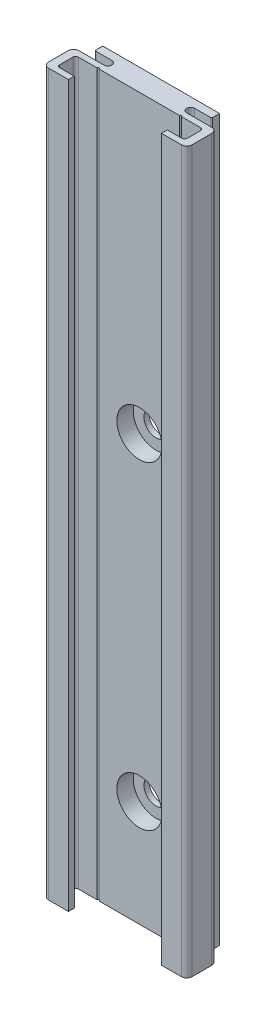
SolidWorks part; units mm, degrees
material "AISI 1035 Acier (SS)"
ref_plane "Plan de face" through (0, 0, 0) normal (0, 0, 1) x (1, 0, 0)
ref_plane "Plan de dessus" through (0, 0, 0) normal (0, 1, 0) x (1, 0, 0)
ref_plane "Plan de droite" through (0, 0, 0) normal (1, 0, 0) x (0, 0, -1)
ref_plane "Plan1" through (0, 0, 0) normal (0, -1, 0) x (1, 0, 0)
sketch "Esquisse1" plane through (0, 0, 0) normal (0, -1, 0) x (1, 0, 0)
  line L0 (13.5, 8.7) -> (-13.5, 8.7)
  line L1 (-13.5, 8.7) -> (-13.5, 3)
  line L2 (-13.5, 3) -> (-7.8, 3)
  line L3 (-7.8, 1.5) -> (-11, 1.5)
  line L4 (-11, 1.5) -> (-11, 0)
  line L5 (-11, 0) -> (11, 0)
  line L6 (11, 0) -> (11, 1.5)
  line L7 (11, 1.5) -> (7.8, 1.5)
  line L8 (7.8, 3) -> (13.5, 3)
  line L9 (13.5, 3) -> (13.5, 8.7)
  arc A0 (-7.8, 3) -> (-7.8, 1.5) centre (-7.8, 2.25) cw
  arc A1 (7.8, 1.5) -> (7.8, 3) centre (7.8, 2.25) cw
extrude "Boss.-Extru.1" add sketch "Esquisse1" against normal blind 1000
sketch "Esquisse2" plane through (0, 1000, 0) normal (0, 1, 0) x (-1, 0, 0)
  line L0 (8.75, 8.7) -> (-8.75, 8.7)
  line L1 (-8.75, 8.7) -> (-8.75, 7.6)
  line L2 (-8.75, 7.6) -> (-12, 7.6)
  line L3 (-12, 7.6) -> (-12, 4.1)
  line L4 (-12, 4.1) -> (12, 4.1)
  line L5 (12, 4.1) -> (12, 7.6)
  line L6 (12, 7.6) -> (8.75, 7.6)
  line L7 (8.75, 7.6) -> (8.75, 8.7)
extrude "Enlèv. mat.-Extru.1" cut sketch "Esquisse2" against normal through all
hole_wizard "Chambrage pour vis à tête hexagonale M41" positions "Esquisse4" profile "Esquisse3" counterbore size "M4" standard "Ansi Metric"
sketch "Esquisse4" plane through (0, 0, 4.1) normal (0, 0, 1) x (1, 0, 0)
  point P0 (0, 980)
  point P1 (0, 920)
  point P2 (0, 860)
  point P3 (0, 800)
  point P4 (0, 740)
  point P5 (0, 680)
  point P6 (0, 620)
  point P7 (0, 560)
  point P8 (0, 500)
  point P9 (0, 440)
  point P10 (0, 380)
  point P11 (0, 320)
  point P12 (0, 260)
  point P13 (0, 200)
  point P14 (0, 140)
  point P15 (0, 80)
  point P16 (0, 20)
sketch "Esquisse3" plane through (0, 980, 4.1) normal (1, 0, 0) x (0, -1, 0)
  line L0 (0, 0) -> (0, 4.1)
  line L1 (0, 4.1) -> (2.25, 4.1)
  line L3 (2.25, 4.1) -> (2.25, 3.1)
  line L4 (2.25, 3.1) -> (4.25, 3.1)
  line L5 (4.25, 3.1) -> (4.25, 0)
  line L7 (4.25, 0) -> (0, 0)
  line L11 (0, -6.35) -> (0, 107.95) construction
  dimension "Diamètre du perçage jusqu'au prochain" = 4.5
  dimension "Profondeur du perçage jusqu'au prochain" = 4.1
  dimension "Diamètre du chambrage" = 8.5
  dimension "Profondeur du chambrage" = 3.1
hole_wizard "Diamètre du perçage Ø0.4 (0.4)1" positions "Esquisse6" profile "Esquisse5" hole size "Ø0.4" standard "Ansi Metric"
sketch "Esquisse6" plane through (0, 0, 0) normal (0, -1, 0) x (-1, 0, 0)
  point P0 (7.75, -4.1)
  point P1 (-7.75, -4.1)
sketch "Esquisse5" plane through (-7.75, 0, 4.1) normal (1, 0, 0) x (0, 0, -1)
  line L0 (0, 0) -> (0, 1000)
  line L1 (0, 1000) -> (0.2, 1000)
  line L2 (0.2, 1000) -> (0.2, 0)
  line L5 (0.2, 0) -> (0, 0)
  line L11 (0, -6.35) -> (0, 107.95) construction
  dimension "Diamètre du perçage jusqu'au prochain" = 0.4
  dimension "Profondeur du perçage jusqu'au prochain" = 1000
fillet "Congé1" radius 0.2 2 edges at (11, 500, 1.5) (-11, 500, 1.5)
fillet "Congé2" radius 0.5 4 edges at (12, 500, 7.6) (12, 500, 4.1) (-12, 500, 7.6) (-12, 500, 4.1)
fillet "Congé3" radius 1 4 edges at (13.5, 500, 3) (13.5, 500, 8.7) (-13.5, 500, 3) (-13.5, 500, 8.7)
sketch "Esquisse9" plane through (0, 0, 0) normal (0, 0, 1) x (1, 0, 0)
  line L0 (-13.5, 0) -> (-13.5, 1000) construction
  line L1 (-13.5, 135.62) -> (13.5, 135.62)
  line L2 (-13.5, 135.62) -> (-13.5, 1000)
  line L3 (-13.5, 1000) -> (13.5, 1000)
  line L4 (13.5, 135.62) -> (13.5, 1000)
  line L5 (13.5, 1000) -> (13.5, 0) construction
  line L6 (7.55, 1000) -> (-7.55, 1000) construction
  dimension "D1" = 135.62
extrude "Enlèv. mat.-Extru.2" cut sketch "Esquisse9" against normal through all both and the other way through all
